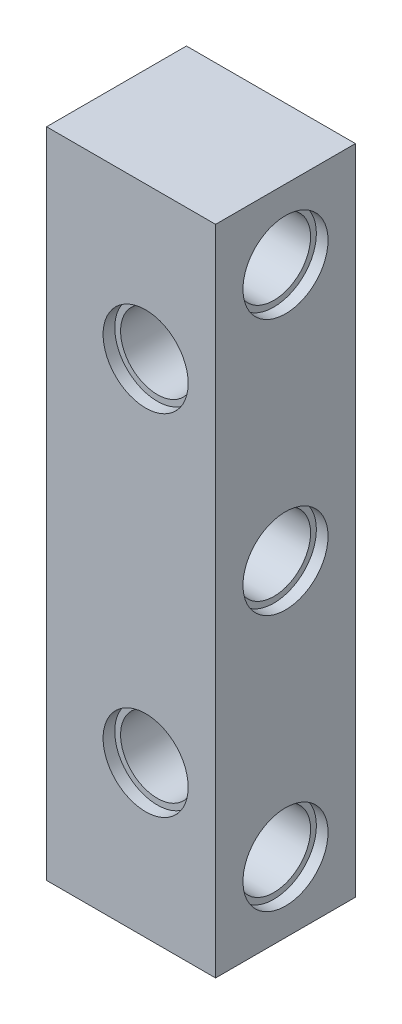
SolidWorks part; units mm, degrees
ref_plane "Front" through (0, 0, 0) normal (0, 0, 1) x (1, 0, 0)
ref_plane "Top" through (0, 0, 0) normal (0, 1, 0) x (1, 0, 0)
ref_plane "Right" through (0, 0, 0) normal (1, 0, 0) x (0, 0, -1)
sketch "Esquisse1" plane through (0, 0, 0) normal (0, 0, 1) x (1, 0, 0)
  line L1 (0, 0) -> (12, 0)
  line L2 (0, 0) -> (0, 40)
  line L3 (0, 40) -> (12, 40)
  line L4 (12, 0) -> (12, 40)
  dimension "D1" = 12
  dimension "D2" = 40
extrude "Boss.-Extru.1" add sketch "Esquisse1" along normal blind 12
sketch "Esquisse3" plane through (0, 0, 12) normal (0, 0, 1) x (1, 0, 0)
  line L0 (5, 40) -> (5, 0) construction
  line L2 (0, 0) -> (12, 0) construction
  line L3 (12, 40) -> (0, 40) construction
  line L4 (0, 40) -> (0, 0) construction
  circle A0 centre (5, 5) radius 3.15
  circle A1 centre (5, 35) radius 3.15
  dimension "D1" = 30
  dimension "D2" = 5
  dimension "D3" = 6.3
  dimension "D4" = 5
extrude "Enlèv. mat.-Extru.1" cut sketch "Esquisse3" against normal through all both and the other way through all
sketch "Esquisse4" plane through (12, 0, 0) normal (1, 0, 0) x (0, 0, -1)
  line L0 (-6, 0) -> (-6, 40) construction
  line L1 (-12, 0) -> (0, 0) construction
  line L2 (-12, 40) -> (0, 40) construction
  circle A0 centre (-6, 20) radius 3.15
  dimension "D1" = 6.3
extrude "Enlèv. mat.-Extru.2" cut sketch "Esquisse4" against normal through all both and the other way through all
sketch "Esquisse5" plane through (0, 0, 12) normal (0, 0, 1) x (1, 0, 0)
  circle A0 centre (5, 35) radius 3.65
  circle A1 centre (5, 5) radius 3.65
  dimension "D1" = 7.3
extrude "Enlèv. mat.-Extru.3" cut sketch "Esquisse5" against normal blind 1
sketch "Esquisse6" plane through (12, 0, 0) normal (1, 0, 0) x (0, 0, -1)
  circle A0 centre (-6, 20) radius 3.65
  dimension "D1" = 7.3
extrude "Enlèv. mat.-Extru.4" cut sketch "Esquisse6" against normal blind 1
sketch "Esquisse7" plane through (12, 0, 0) normal (1, 0, 0) x (0, 0, -1)
  line L1 (-12, 0) -> (-12, 40) construction
  line L2 (0, 0) -> (-12, 0)
  line L3 (0, 0) -> (0, -8)
  line L4 (0, -8) -> (-12, -8)
  line L5 (-12, 0) -> (-12, -8)
  line L6 (-12, 20) -> (0, 20) construction
  line L7 (0, 0) -> (0, 40) construction
  line L8 (-12, 40) -> (-12, 48)
  line L9 (0, 48) -> (-12, 48)
  line L10 (0, 40) -> (0, 48)
  line L11 (0, 40) -> (-12, 40)
  dimension "D1" = 8
extrude "Boss.-Extru.2" add sketch "Esquisse7" against normal up to vertex (12 mm away)
sketch "Esquisse8" plane through (0, -8, 0) normal (0, -1, 0) x (1, 0, 0)
  line L0 (0, 12) -> (12, 12) construction
  line L1 (12, 0) -> (11, 0)
  line L2 (12, 0) -> (12, 12)
  line L3 (12, 12) -> (11, 12)
  line L4 (11, 0) -> (11, 12)
  dimension "D1" = 1
extrude "Enlèv. mat.-Extru.5" cut sketch "Esquisse8" against normal through all both and the other way through all
sketch "Esquisse9" plane through (11, 0, 0) normal (1, 0, 0) x (0, 0, -1)
  line L0 (-12, 20) -> (0, 20) construction
  line L1 (-12, 48) -> (-12, -8) construction
  line L2 (0, 48) -> (0, -8) construction
  line L3 (-6, 20) -> (-6, 42) construction
  circle A0 centre (-6, 42) radius 3.15
  circle A1 centre (-6, 20) radius 3.15 construction
  circle A2 centre (-6, -2) radius 3.15
  dimension "D1" = 22
extrude "Enlèv. mat.-Extru.6" cut sketch "Esquisse9" against normal through all both and the other way through all
sketch "Esquisse10" plane through (0, 0, 0) normal (-1, 0, 0) x (0, 0, 1)
  circle A0 centre (6, 42) radius 3.65
  circle A1 centre (6, -2) radius 3.65
  circle A2 centre (6, 20) radius 3.65
  dimension "D1" = 7.3
extrude "Enlèv. mat.-Extru.7" [suppressed] cut sketch "Esquisse10" against normal blind 1
sketch "Esquisse11" plane through (0, 0, 0) normal (-1, 0, 0) x (0, 0, 1)
  line L4 (0, 48) -> (0, -8)
  line L5 (0, -8) -> (12, -8)
  line L6 (12, -8) -> (12, 48)
  line L7 (12, 48) -> (0, 48)
  line L8 (0, 48) -> (0, -8)
  line L9 (0, -8) -> (12, -8)
  line L10 (12, -8) -> (12, 48)
  line L11 (12, 48) -> (0, 48)
  circle A0 centre (6, -2) radius 3.15 construction
  circle A1 centre (6, 20) radius 3.15 construction
  circle A2 centre (6, 42) radius 3.15 construction
  circle A3 centre (6, -2) radius 3.15
  circle A4 centre (6, 20) radius 3.15
  circle A5 centre (6, 42) radius 3.15
  dimension "D1" = 0
extrude "Boss.-Extru.3" add sketch "Esquisse11" along normal blind 3.5
sketch "Esquisse12" plane through (-3.5, 0, 0) normal (-1, 0, 0) x (0, 0, 1)
  circle A0 centre (6, 42) radius 3.65
  circle A1 centre (6, 20) radius 3.65
  circle A2 centre (6, -2) radius 3.65
  dimension "D1" = 7.3
extrude "Enlèv. mat.-Extru.8" cut sketch "Esquisse12" against normal blind 1
sketch "Esquisse13" plane through (11, 0, 0) normal (1, 0, 0) x (0, 0, -1)
  circle A0 centre (-6, -2) radius 3.65
  circle A1 centre (-6, 20) radius 3.65
  circle A2 centre (-6, 42) radius 3.65
  dimension "D1" = 7.3
extrude "Enlèv. mat.-Extru.9" cut sketch "Esquisse13" against normal blind 1
